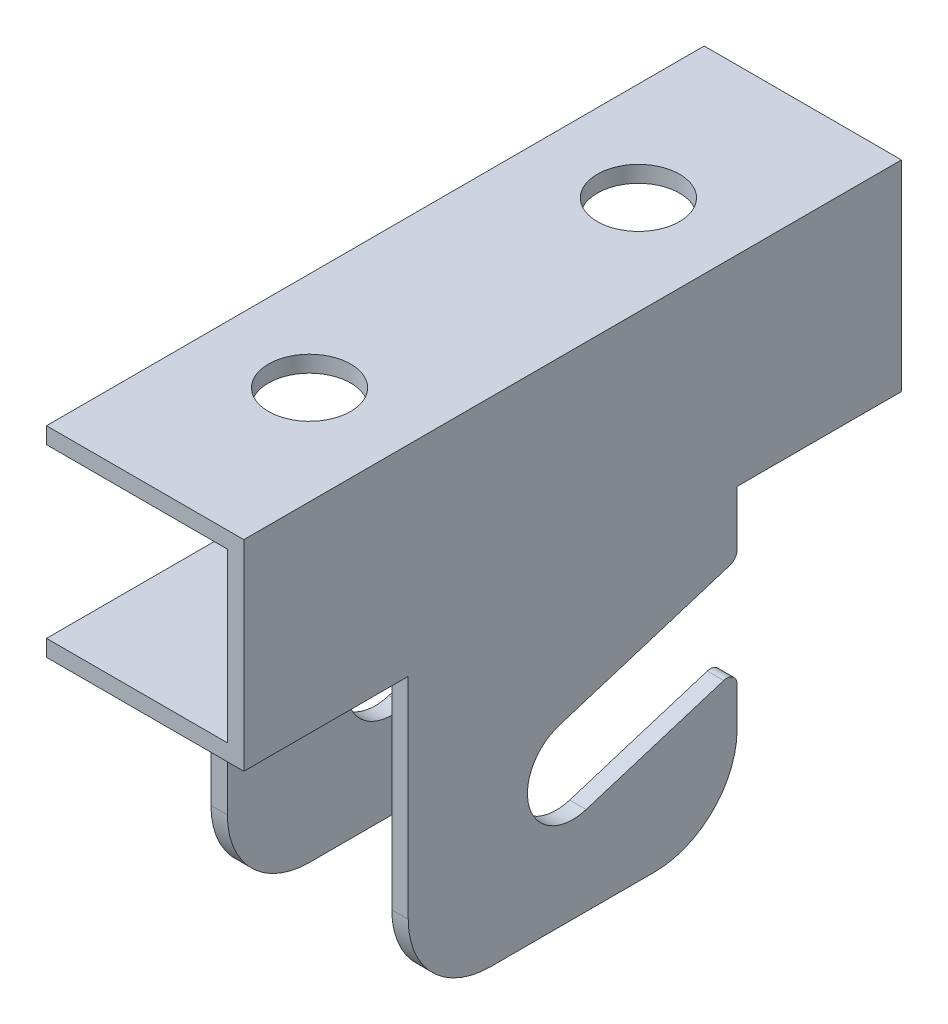
SolidWorks part; units mm, degrees
material "AISI 1015 Steel, Cold Drawn (SS)"
ref_plane "Front Plane" through (0, 0, 0) normal (0, 0, 1) x (1, 0, 0)
ref_plane "Top Plane" through (0, 0, 0) normal (0, 1, 0) x (1, 0, 0)
ref_plane "Right Plane" through (0, 0, 0) normal (1, 0, 0) x (0, 0, -1)
other "Configuration Table"
sketch "Sketch1" plane through (0, 0, 0) normal (0, 0, 1) x (1, 0, 0)
  line L1 (0, 76.2) -> (30.48, 76.2)
  line L2 (30.48, 76.2) -> (30.48, 73.66)
  line L3 (27.94, 73.66) -> (0, 73.66)
  line L5 (0, 47.752) -> (27.94, 47.752)
  line L6 (30.48, 47.752) -> (30.48, 0)
  line L7 (30.48, 0) -> (27.94, 0)
  line L8 (27.94, 0) -> (27.94, 45.212)
  line L9 (27.94, 45.212) -> (2.54, 45.212)
  line L10 (2.54, 45.212) -> (2.54, 0)
  line L11 (2.54, 0) -> (0, 0)
  line L12 (30.48, 73.66) -> (30.48, 47.752)
  line L13 (27.94, 47.752) -> (27.94, 73.66)
  line L14 (0, 76.2) -> (0, 73.66)
  line L15 (0, 0) -> (0, 47.752)
  point P13 (30.48, 74.93)
  dimension "D1" = 76.2
  dimension "D2" = 30.48
  dimension "D3" = 2.54
  dimension "D4" = 2.54
  dimension "D6" = 25.908
extrude "Boss-Extrude1" add sketch "Sketch1" along normal mid plane 101.6
sketch "Sketch4" plane through (30.48, 0, 0) normal (1, 0, 0) x (0, 0, -1)
  line L0 (-50.8, 0) -> (50.8, 0) construction
  line L1 (-50.8, 45.212) -> (-25.4, 45.212)
  line L2 (-50.8, 45.212) -> (-50.8, 0)
  line L3 (-50.8, 0) -> (-25.4, 0)
  line L4 (-25.4, 45.212) -> (-25.4, 0)
  line L6 (50.8, 45.212) -> (25.4, 45.212)
  line L7 (50.8, 45.212) -> (50.8, 0)
  line L8 (50.8, 0) -> (25.4, 0)
  line L9 (25.4, 45.212) -> (25.4, 0)
  dimension "D1" = 25.4
  dimension "D2" = 25.4
extrude "Cut-Extrude1" cut sketch "Sketch4" against normal through all both and the other way through all
sketch "Sketch7" plane through (30.48, 0, 0) normal (1, 0, 0) x (0, 0, -1)
  line L0 (-25.4, 0) -> (25.4, 0) construction
  line L1 (-2.08, 26.9881) -> (25.4, 35.56)
  line L2 (25.4, 0) -> (25.4, 45.212) construction
  line L3 (2.08, 13.6519) -> (25.4, 20.9261)
  line L4 (25.4, 45.212) -> (50.8, 45.212) construction
  line L5 (25.4, 35.56) -> (25.4, 20.9261)
  line L6 (-25.4, 45.212) -> (-25.4, 0) construction
  arc A0 (-2.08, 26.9881) -> (2.08, 13.6519) centre (0, 20.32) ccw
  dimension "D2" = 13.97
  dimension "D1" = 20.32
  dimension "D3" = 9.652
  dimension "D4" = 25.4
extrude "Cut-Extrude4" cut sketch "Sketch7" against normal through all both and the other way through all
sketch "Sketch8" plane through (0, 76.2, 0) normal (0, 1, 0) x (1, 0, 0)
  line L0 (27.94, -50.8) -> (27.94, 50.8) construction
  line L1 (30.48, 50.8) -> (0, 50.8) construction
  circle A0 centre (15.24, -25.4) radius 6.35
  circle A1 centre (15.24, 25.4) radius 6.35
  dimension "D4" = 12.7
  dimension "D1" = 12.7
  dimension "D2" = 50.8
  dimension "D3" = 25.4
extrude "BOLT HOLES" cut sketch "Sketch8" against normal through all both
fillet "Fillet3" radius 12.7 4 edges at (29.21, 0, 25.4) (1.27, 0, 25.4) (1.27, 0, -25.4) (29.21, 0, -25.4)
fillet "Fillet4" radius 1.5875 4 edges at (1.27, 35.56, -25.4) (29.21, 35.56, -25.4) (1.27, 20.9261, -25.4) (29.21, 20.9261, -25.4)
equation "\"A\"= 3"
equation "\"B\"= 1"
